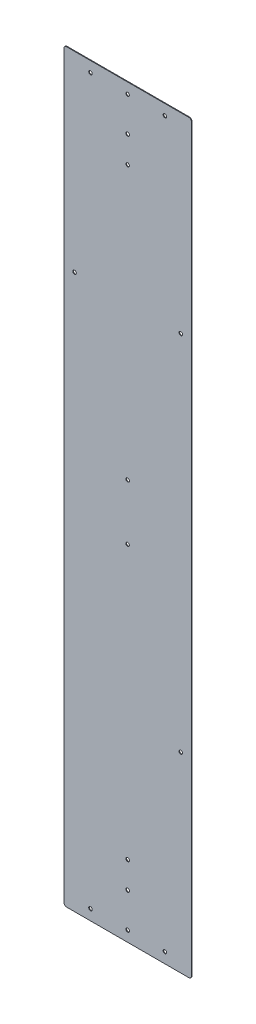
SolidWorks part; units mm, degrees
material "Acrylic (Medium-high impact)"
ref_plane "Front Plane" through (0, 0, 0) normal (0, 0, 1) x (1, 0, 0)
ref_plane "Top Plane" through (0, 0, 0) normal (0, 1, 0) x (1, 0, 0)
ref_plane "Right Plane" through (0, 0, 0) normal (1, 0, 0) x (0, 0, -1)
sketch "Sketch1" plane through (0, 0, 0) normal (0, 0, 1) x (1, 0, 0)
  line L1 (-152.4, 890.5875) -> (152.4, 890.5875)
  line L2 (-152.4, 890.5875) -> (-152.4, -890.5875)
  line L3 (-152.4, -890.5875) -> (152.4, -890.5875)
  line L4 (152.4, 890.5875) -> (152.4, -890.5875)
  line L5 (-152.4, 890.5875) -> (152.4, -890.5875) construction
  line L6 (-152.4, -890.5875) -> (152.4, 890.5875) construction
  point P0 (0, 0)
  dimension "D1" = 1781.175
  dimension "D2" = 304.8
extrude "Boss-Extrude1" add sketch "Sketch1" along normal blind 1.5875
sketch "Sketch2" plane through (0, 0, 1.5875) normal (0, 0, 1) x (1, 0, 0)
  line L0 (-152.4, 0) -> (152.4, 0) construction
  line L1 (-152.4, 890.5875) -> (-152.4, -890.5875) construction
  line L2 (152.4, -890.5875) -> (152.4, 890.5875) construction
  line L3 (152.4, 890.5875) -> (-152.4, 890.5875) construction
  line L4 (88.9, 865.1875) -> (-88.9, 865.1875)
  line L5 (88.9, -865.1875) -> (-88.9, -865.1875)
  point P0 (0, 865.1875)
  point P3 (0, 66.675)
  point P4 (-127, 433.3875)
  point P6 (127, 433.3875)
  point P12 (0, 719.1375)
  point P15 (0, -865.1875)
  point P16 (127, -433.3875)
  point P17 (-127, -433.3875)
  point P18 (0, -66.675)
  point P19 (0, -719.1375)
  point P20 (0, -782.6375)
  point P21 (0, 782.6375)
  point P24 (0, 865.1875)
  dimension "D1" = 25.4
  dimension "D2" = 25.4
  dimension "D3" = 25.4
  dimension "D4" = 66.675
  dimension "D5" = 457.2
  dimension "D6" = 63.5
  dimension "D7" = 107.95
  dimension "D8" = 177.8
hole_wizard "5/16 Clearance Hole1" positions "Sketch3" profile "Sketch4" hole size "5/16" standard "ANSI Inch" end condition up to next
sketch "Sketch3" plane through (0, 0, 1.5875) normal (0, 0, 1) x (1, 0, 0)
  point P0 (0, 865.1875)
  point P3 (-127, 433.3875)
  point P6 (127, 433.3875)
  point P9 (0, 66.675)
  point P12 (0, -66.675)
  point P18 (127, -433.3875)
  point P21 (0, -865.1875)
  point P25 (0, 782.6375)
  point P28 (0, 719.1375)
  point P31 (0, -782.6375)
  point P34 (0, -719.1375)
  point P37 (-88.9, 865.1875)
  point P40 (88.9, 865.1875)
  point P43 (-88.9, -865.1875)
  point P46 (88.9, -865.1875)
sketch "Sketch4" plane through (0, 865.1875, 1.5875) normal (1, 0, 0) x (0, -1, 0)
  line L0 (0, 0) -> (0, 1.5875)
  line L1 (0, 1.5875) -> (4.2164, 1.5875)
  line L2 (4.2164, 1.5875) -> (4.2164, 0)
  line L5 (4.2164, 0) -> (0, 0)
  line L11 (0, -6.35) -> (0, 107.95) construction
  dimension "Thru Hole Dia." = 8.4328
  dimension "Thru Hole Depth" = 1.5875
sketch "Sketch5" plane through (0, 0, 1.5875) normal (0, 0, 1) x (1, 0, 0)
  line L0 (152.4, -890.5875) -> (152.4, 890.5875) construction
  line L1 (152.4, -558.8) -> (0, -558.8)
  line L2 (152.4, -558.8) -> (152.4, -279.4)
  line L3 (152.4, -279.4) -> (0, -279.4)
  line L4 (0, -558.8) -> (0, -279.4)
  line L5 (-152.4, 0) -> (152.4, 0) construction
  dimension "D1" = 558.8
  dimension "D2" = 279.4
  dimension "D3" = 152.4
sketch "Sketch7" plane through (0, 0, 1.5875) normal (0, 0, 1) x (1, 0, 0)
  line L4 (0, -558.8) -> (152.4, -558.8)
  line L5 (0, -279.4) -> (0, -558.8)
  line L6 (152.4, -279.4) -> (0, -279.4)
  line L7 (152.4, -558.8) -> (152.4, -279.4)
  line L8 (0, -558.8) -> (152.4, -558.8)
  line L9 (0, -279.4) -> (0, -558.8)
  line L10 (152.4, -279.4) -> (0, -279.4)
  line L11 (152.4, -558.8) -> (152.4, -279.4)
  dimension "D1" = 0
extrude "Cut-Extrude2" [suppressed] cut sketch "Sketch7" against normal through all
fillet "Fillet1" [suppressed] radius 12.7
sketch "Sketch8" plane through (0, 0, 1.5875) normal (0, 0, 1) x (1, 0, 0)
  line L0 (0, -55) -> (0, 55) construction
  line L1 (-152.4, -558.8) -> (-152.4, -279.4) construction
  line L2 (-152.4, -279.4) -> (0, -279.4)
  line L3 (0, -279.4) -> (0, -558.8)
  line L4 (0, -558.8) -> (152.4, -558.8)
  line L5 (0, -279.4) -> (0, -558.8)
  line L6 (152.4, -279.4) -> (0, -279.4)
  line L7 (152.4, -558.8) -> (152.4, -279.4)
  line L8 (-152.4, -558.8) -> (152.4, -558.8) construction
  line L9 (0, -279.4) -> (0, -558.8) construction
  line L10 (152.4, -279.4) -> (-152.4, -279.4) construction
  line L11 (152.4, -558.8) -> (152.4, -279.4) construction
  line L12 (0, -558.8) -> (-152.4, -558.8)
  line L13 (-152.4, -558.8) -> (-152.4, -279.4)
  dimension "D1" = 0
extrude "Cut-Extrude3" [suppressed] cut sketch "Sketch8" against normal through all
fillet "Fillet2" [suppressed] radius 12.7
sketch "Sketch9" [suppressed] plane through (0, 0, 1.5875) normal (0, 0, 1) x (1, 0, 0)
  line L0 (-152.4, 890.5875) -> (-152.4, -890.5875) construction
  line L1 (-152.4, -279.4) -> (50.8, -279.4)
  line L2 (-152.4, -279.4) -> (-152.4, -558.8)
  line L3 (-152.4, -558.8) -> (50.8, -558.8)
  line L4 (50.8, -279.4) -> (50.8, -558.8)
  line L5 (152.4, -558.8) -> (0, -558.8) construction
  line L6 (152.4, -279.4) -> (0, -279.4) construction
  dimension "D1" = 203.2
extrude "Cut-Extrude4" [suppressed] cut sketch "Sketch9" against normal through all
fillet "Fillet3" [suppressed] radius 12.7
fillet "Fillet4" radius 6.35 4 edges at (-152.4, 890.5875, 0.7937) (152.4, 890.5875, 0.7937) (152.4, -890.5875, 0.7937) (-152.4, -890.5875, 0.7937)
